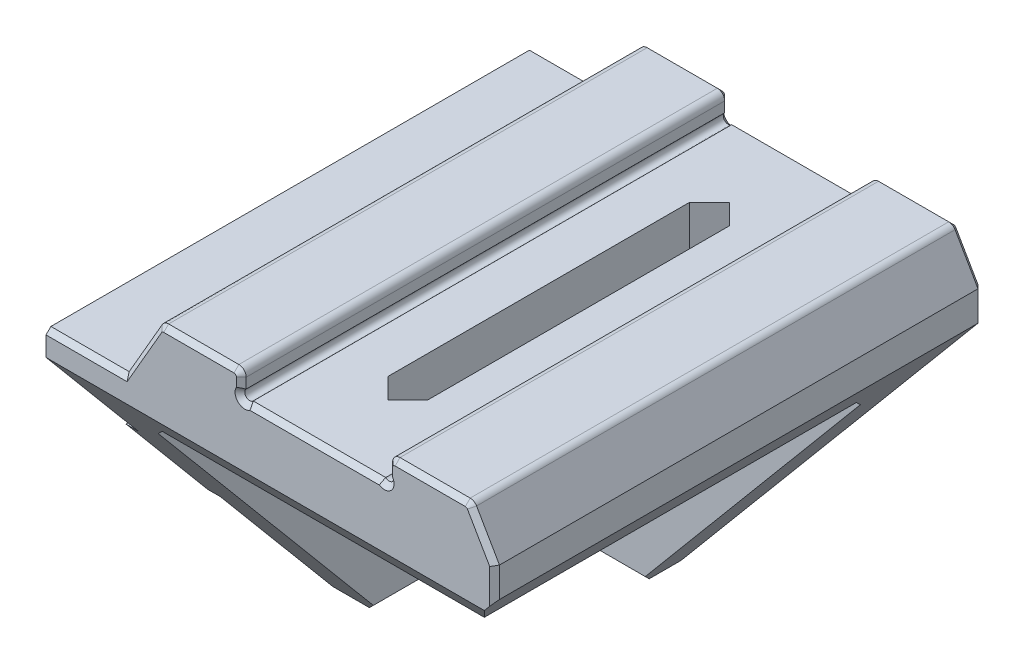
SolidWorks part; units mm, degrees
ref_plane "Front Plane" through (0, 0, 0) normal (0, 0, 1) x (1, 0, 0)
ref_plane "Top Plane" through (0, 0, 0) normal (0, 1, 0) x (1, 0, 0)
ref_plane "Right Plane" through (0, 0, 0) normal (1, 0, 0) x (0, 0, -1)
sketch "Sketch1" plane through (0, 0, 0) normal (0, 0, 1) x (1, 0, 0)
  line L0 (0, 0) -> (0, -30)
  line L1 (0, 0) -> (6.4132, 0)
  line L2 (6.4132, 0) -> (9.3, 5)
  line L3 (9.3, 5) -> (16, 5)
  line L4 (16, 5) -> (16, 3.5573)
  line L5 (16, 3) -> (16.574, 3) construction
  line L6 (28, 3) -> (28, 3.5657) construction
  line L7 (28, 5) -> (34.7, 5)
  line L8 (34.7, 5) -> (37.5868, 0)
  line L9 (0, -30) -> (12.4138, -30)
  line L10 (12.4138, -30) -> (37.5868, 0)
  line L11 (16, 3) -> (16.574, 3.5573) construction
  line L12 (16, 3.5573) -> (16, 3) construction
  line L13 (16.574, 3) -> (27.4343, 3)
  line L14 (28, 3) -> (27.4343, 3.5657) construction
  line L15 (28, 3.5657) -> (28, 5)
  line L16 (27.4343, 3) -> (28, 3) construction
  arc A0 (16, 3.5573) -> (16.574, 3) centre (16.287, 3.2786) ccw
  arc A1 (16.574, 3) -> (16, 3.5573) centre (16.287, 3.2786) ccw construction
  arc A2 (27.4343, 3) -> (28, 3.5657) centre (27.7172, 3.2828) ccw
  arc A3 (28, 3.5657) -> (27.4343, 3) centre (27.7172, 3.2828) ccw construction
  point P13 (0, 0)
  point P15 (27.5696, 2.4017)
  point P16 (0, 0)
  point P19 (0, 0)
  point P20 (27.9075, 2.4709)
  point P26 (28, 2.408)
  point P27 (27.9575, 2.4433)
  point P28 (27.5757, 1.9837)
  point P29 (27.5948, 1.9662)
  dimension "D13" = 0.8
  dimension "D15" = 0.8
  dimension "D1" = 30
  dimension "D2" = 9.3
  dimension "D3" = 60
  dimension "D4" = 3
  dimension "D5" = 6.7
  dimension "D6" = 2
  dimension "D7" = 12
  dimension "D8" = 2
  dimension "D9" = 6.7
  dimension "D10" = 5
  dimension "D11" = 60
  dimension "D12" = 130
  dimension "D14" = 44.152
  dimension "D16" = 45
extrude "Boss-Extrude1" add sketch "Sketch1" along normal blind 40
sketch "Sketch2" plane through (0, 0, 40) normal (0, 0, 1) x (1, 0, 0)
  line L0 (5, -30) -> (5, -5)
  line L1 (0, -30) -> (12.4138, -30) construction
  line L2 (5, -5) -> (33.3913, -5)
  line L3 (12.4138, -30) -> (37.5868, 0) construction
  line L4 (0, 0) -> (0, -30) construction
  line L5 (6.4132, 0) -> (0, 0) construction
  line L17 (6.4132, 0) -> (0, 0)
  line L18 (0, 0) -> (0, -30)
  line L19 (0, -30) -> (12.4138, -30)
  line L20 (12.4138, -30) -> (37.5868, 0)
  line L21 (37.5868, 0) -> (34.7, 5)
  line L22 (34.7, 5) -> (28, 5)
  line L23 (28, 5) -> (28, 3.5657)
  line L24 (27.4343, 3) -> (16.574, 3)
  line L25 (16, 3.5573) -> (16, 5)
  line L26 (16, 5) -> (9.3, 5)
  line L27 (9.3, 5) -> (6.4132, 0)
  line L28 (6.4132, 0) -> (0, 0)
  line L29 (0, 0) -> (0, -30)
  line L30 (0, -30) -> (12.4138, -30)
  line L31 (12.4138, -30) -> (37.5868, 0)
  line L32 (37.5868, 0) -> (34.7, 5)
  line L33 (34.7, 5) -> (28, 5)
  line L36 (16, 3.5573) -> (16, 5)
  line L37 (16, 5) -> (9.3, 5)
  line L38 (9.3, 5) -> (6.4132, 0)
  line L39 (27.4343, 3) -> (16.574, 3)
  line L40 (28, 5) -> (28, 3.5657)
  arc A1 (16, 3.5573) -> (16.574, 3) centre (16.287, 3.2786) ccw
  arc A2 (16, 3.5573) -> (16.574, 3) centre (16.287, 3.2786) ccw
  arc A4 (27.4343, 3) -> (28, 3.5657) centre (27.7172, 3.2828) ccw
  arc A5 (27.4343, 3) -> (28, 3.5657) centre (27.7172, 3.2828) ccw
  line M5 (0, -30) -> (12.4138, -30)
  line M6 (12.4138, -30) -> (37.5868, 0)
  dimension "D1" = 5
  dimension "D2" = 5
  dimension "D3" = 0
extrude "Cut-Extrude1" cut sketch "Sketch2" against normal blind 35 contours L2 L0 M5 M6
sketch "Sketch3" plane through (0, 0, 0) normal (-1, 0, 0) x (0, 0, 1)
  line L0 (40, -2) -> (16.5052, -30)
  line L1 (40, 0) -> (40, -30) construction
  line L2 (40, -30) -> (0, -30) construction
  line L7 (0, 0) -> (0, -30)
  line L8 (0, -30) -> (40, -30)
  line L9 (40, -30) -> (40, 0)
  line L10 (40, 0) -> (0, 0)
  line L11 (0, 0) -> (0, -30)
  line L12 (0, -30) -> (40, -30)
  line L13 (40, -30) -> (40, 0)
  line L14 (40, 0) -> (0, 0)
  line M7 (0, -30) -> (40, -30)
  line M8 (40, -30) -> (40, 0)
  dimension "D1" = 2
  dimension "D2" = 130
  dimension "D3" = 0
extrude "Cut-Extrude2" cut sketch "Sketch3" against normal through all contours L0 M8 M7
sketch "Sketch4" plane through (0, 0, 0) normal (-1, 0, 0) x (0, 0, 1)
  line L0 (0, -19) -> (25.7353, -19)
  line L1 (0, 0) -> (0, -30) construction
  line L2 (40, -2) -> (16.5052, -30) construction
  line L3 (0, -11) -> (32.4481, -11)
  line L4 (16.5052, -30) -> (0, -30) construction
  line L10 (0, -30) -> (16.5052, -30)
  line L11 (16.5052, -30) -> (40, -2)
  line L12 (40, -2) -> (40, 0)
  line L13 (40, 0) -> (0, 0)
  line L14 (0, 0) -> (0, -30)
  line L15 (0, -30) -> (16.5052, -30)
  line L16 (16.5052, -30) -> (40, -2)
  line L17 (40, -2) -> (40, 0)
  line L18 (40, 0) -> (0, 0)
  line L19 (0, 0) -> (0, -30)
  line M9 (16.5052, -30) -> (40, -2)
  line M12 (0, 0) -> (0, -30)
  dimension "D1" = 11
  dimension "D2" = 8
  dimension "D3" = 0
extrude "Boss-Extrude2" add sketch "Sketch4" along normal blind 1 contours L3 L0 M12 M9
sketch "Sketch5" plane through (-1, 0, 0) normal (-1, 0, 0) x (0, 0, 1)
  line L0 (0, -15) -> (29.0917, -15) construction
  line L1 (0, -11) -> (0, -19) construction
  line L2 (25.7353, -19) -> (32.4481, -11) construction
  circle A0 centre (14.5459, -15) radius 1.6
  dimension "D1" = 3.2
extrude "Cut-Extrude3" cut sketch "Sketch5" against normal through all
chamfer "Chamfer2" distance 1.3 angle 40 1 edges at (37.5868, 0, 20)
fillet "Fillet1" radius 0.6 4 edges at (34.7, 5, 20) (16, 5, 20) (9.3, 5, 20) (28, 5, 20)
sketch "Sketch6" plane through (0, 3, 0) normal (0, 1, 0) x (1, 0, 0)
  line L0 (22.0042, 0) -> (22.0042, -40) construction
  line L3 (22.0042, -34) -> (22.0042, -6) construction
  line L4 (22.0042, -6) -> (20.3542, -7.65)
  line L5 (20.3542, -7.65) -> (20.3542, -32.35)
  line L6 (20.3542, -32.35) -> (22.0042, -34)
  line L7 (23.6542, -32.35) -> (22.0042, -34)
  line L8 (23.6542, -7.65) -> (23.6542, -32.35)
  line L9 (22.0042, -6) -> (23.6542, -7.65)
  line L10 (27.4343, 0) -> (16.574, 0) construction
  line L11 (27.4343, -40) -> (16.574, -40) construction
  point P2 (22.0031, 0)
  point P5 (22.0031, -40)
  point P9 (22.0042, -20)
  dimension "D1" = 28
  dimension "D2" = 135
  dimension "D3" = 135
  dimension "D4" = 1.65
extrude "Cut-Extrude4" cut sketch "Sketch6" against normal through all
sketch "Sketch7" plane through (0, -5, 0) normal (0, -1, 0) x (1, 0, 0)
  line L0 (5, 5) -> (33.3913, 5) construction
  line L1 (18.0042, 5) -> (26.0042, 5)
  line L2 (18.0042, 5) -> (18.0042, 36)
  line L3 (18.0042, 36) -> (26.0042, 36)
  line L4 (26.0042, 5) -> (26.0042, 36)
  point P6 (22.0042, 36)
  dimension "D1" = 8
  dimension "D2" = 31
extrude "Cut-Extrude5" cut sketch "Sketch7" against normal blind 3
chamfer "Chamfer3" distance 2 6 edges at (29.6977, -5, 5) (8.7069, -30, 5) (5, -30, 10.7526) (5, -17.5, 5) (11.5021, -5, 5) (5, -5, 21.2414)
chamfer "Chamfer4" distance 0.4 angle 45 37 edges at (3.2066, 0, 0) (3.2066, 0, 40) (16, 3.9786, 0) (16, 3.9786, 40) (7.77, 2.35, 40) (7.77, 2.35, 0) (15.8243, 4.8243, 40) (15.8243, 4.8243, 0) (9.3464, 4.9196, 40) (9.3464, 4.9196, 0) (12.5232, 5, 40) (12.5232, 5, 0) (31.4768, 5, 40) (31.4768, 5, 0) (34.6536, 4.9196, 40) (34.6536, 4.9196, 0) (36.7511, 0.2257, 40) (36.7511, 0.2257, 0) (35.8122, 3.0737, 0) (35.8122, 3.0737, 40) (0, -5.5, 0) (-0.5, -11, 0) (-1, -15, 0) (-0.5, -19, 0) (0, -24.5, 0) (6.2069, -30, 0) (24.5824, -15.4979, 0) (22.0042, 3, 0) (22.0042, 3, 40) (16.0084, 2.9916, 0) (16.0084, 2.9916, 40) (28, 3.9828, 40) (28, 3.9828, 0) (28, 3, 0) (28, 3, 40) (28.1757, 4.8243, 40) (28.1757, 4.8243, 0)
mirror "Mirror3" [suppressed] about plane through (0, 0, 0) normal (1, 0, 0)
delete or keep bodies "Body-Delete/Keep 1" [suppressed] type delete bodies bodies 108
